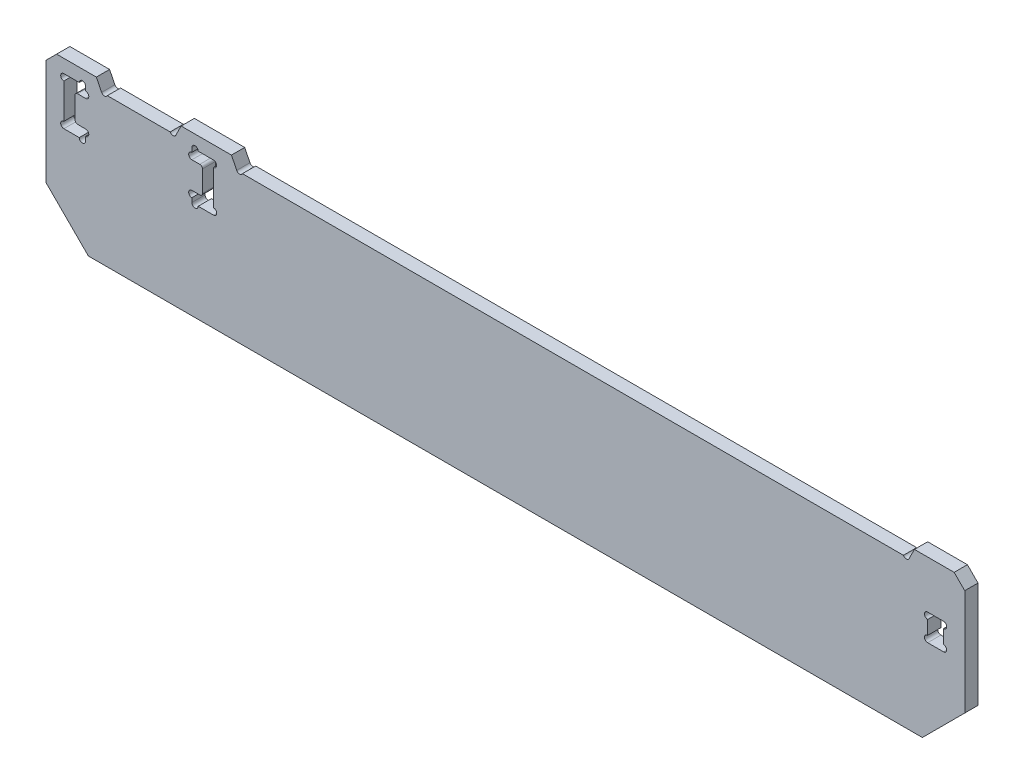
SolidWorks part; units mm, degrees
ref_plane "前视基准面" through (0, 0, 0) normal (0, 0, 1) x (1, 0, 0)
ref_plane "上视基准面" through (0, 0, 0) normal (0, 1, 0) x (1, 0, 0)
ref_plane "右视基准面" through (0, 0, 0) normal (1, 0, 0) x (0, 0, -1)
sketch "草图1" plane through (0, 0, 0) normal (0, 0, 1) x (1, 0, 0)
  line L0 (86.7, 0) -> (-86.7, 0)
  line L1 (-86.7, 0) -> (-86.7, -30)
  line L2 (-86.7, -30) -> (86.7, -30)
  line L3 (86.7, -30) -> (86.7, 0)
  point P4 (0, 0)
  dimension "D1" = 173.4
  dimension "D2" = 30
extrude "凸台-拉伸1" add sketch "草图1" along normal mid plane 2.5
chamfer "倒角1" distance 8 angle 45 2 edges at (86.7, -30, 0) (-86.7, -30, 0)
chamfer "倒角2" distance 2 angle 45 2 edges at (86.7, 0, 0) (-86.7, 0, 0)
sketch "草图2" plane through (0, 0, 1.25) normal (0, 0, 1) x (1, 0, 0)
  line L0 (-77.2, 0) -> (-76.2, -2)
  line L1 (84.7, 0) -> (-84.7, 0) construction
  line L2 (-76.2, -2) -> (-62.2, -2)
  line L3 (-62.2, -2) -> (-61.2, 0)
  line L4 (-61.2, 0) -> (-77.2, 0)
  line L6 (-86.7, -2) -> (-86.7, -22) construction
  point P8 (-69.2, 0)
  dimension "D1" = 2
  dimension "D2" = 16
  dimension "D3" = 14
  dimension "D4" = 17.5
extrude "切除-拉伸1" cut sketch "草图2" against normal through all
sketch "草图6" plane through (0, 0, 1.25) normal (0, 0, 1) x (1, 0, 0)
  line L0 (-51.7, 0) -> (-50.7, -2)
  line L1 (84.7, 0) -> (-61.2, 0) construction
  line L2 (-50.7, -2) -> (76.2, -2)
  line L3 (76.2, -2) -> (77.2, 0)
  line L4 (-51.7, 0) -> (77.2, 0)
  line L5 (-76.2, -2) -> (-62.2, -2) construction
  line L6 (-77.2, 0) -> (-76.2, -2) construction
  point P4 (0, 0)
  dimension "D1" = 7.5
  dimension "D2" = 9.5
extrude "切除-拉伸4" cut sketch "草图6" against normal through all
sketch "草图4" plane through (0, 0, 1.25) normal (0, 0, 1) x (1, 0, 0)
  line L0 (-83.325, -2.5) -> (-79.225, -2.5)
  line L1 (-79.225, -2.5) -> (-79.225, -4.5)
  line L2 (-79.225, -4.5) -> (-81.225, -4.5)
  line L3 (-81.225, -4.5) -> (-81.225, -9.5)
  line L4 (-81.225, -9.5) -> (-79.225, -9.5)
  line L5 (-79.225, -9.5) -> (-79.225, -11.5)
  line L6 (-79.225, -11.5) -> (-83.325, -11.5)
  line L7 (-83.325, -11.5) -> (-83.325, -2.5)
  line L8 (-69.2, -2.5) -> (-69.2, -11.5) construction
  line L9 (-76.2, -2) -> (-62.2, -2) construction
  line L11 (-59.175, -11.5) -> (-55.075, -11.5)
  line L12 (-59.175, -9.5) -> (-59.175, -11.5)
  line L13 (-57.175, -9.5) -> (-59.175, -9.5)
  line L14 (-57.175, -4.5) -> (-57.175, -9.5)
  line L15 (-59.175, -4.5) -> (-57.175, -4.5)
  line L16 (-59.175, -2.5) -> (-59.175, -4.5)
  line L17 (-55.075, -2.5) -> (-59.175, -2.5)
  line L18 (-55.075, -11.5) -> (-55.075, -2.5)
  line L19 (84.7, 0) -> (77.2, 0) construction
  point P10 (0, 0)
  point P13 (-69.2, -2)
  dimension "D1" = 5
  dimension "D2" = 9
  dimension "D3" = 20.05
  dimension "D4" = 2
  dimension "D5" = 2.1
  dimension "D6" = 2.5
extrude "切除-拉伸2" cut sketch "草图4" against normal through all
sketch "草图5" plane through (0, 0, 1.25) normal (0, 0, 1) x (1, 0, 0)
  line L0 (-83.325, -2.5) -> (-83.325, -11.5) construction
  line L1 (-83.325, -11.5) -> (-79.225, -11.5) construction
  line L2 (-79.225, -11.5) -> (-79.225, -9.5) construction
  line L3 (76.2, -2) -> (77.2, 0) construction
  line L4 (-79.225, -2.5) -> (-83.325, -2.5) construction
  line L5 (-55.075, -2.5) -> (-59.175, -2.5) construction
  line L6 (-59.175, -2.5) -> (-59.175, -4.5) construction
  line L7 (-59.175, -9.5) -> (-59.175, -11.5) construction
  line L8 (-59.175, -11.5) -> (-55.075, -11.5) construction
  line L9 (-55.075, -11.5) -> (-55.075, -2.5) construction
  line L10 (-79.225, -4.5) -> (-79.225, -2.5) construction
  line L11 (-51.7, 0) -> (-50.7, -2) construction
  line L12 (-77.2, 0) -> (-76.2, -2) construction
  line L13 (-62.2, -2) -> (-61.2, 0) construction
  circle A0 centre (-83.325, -3.1) radius 0.6
  circle A1 centre (-83.325, -10.9) radius 0.6
  circle A2 centre (-79.825, -11.5) radius 0.6
  circle A3 centre (-79.225, -10.1) radius 0.6
  circle A4 centre (-79.225, -3.9) radius 0.6
  circle A5 centre (-79.825, -2.5) radius 0.6
  circle A6 centre (-58.575, -2.5) radius 0.6
  circle A7 centre (-59.175, -3.9) radius 0.6
  circle A8 centre (-59.175, -10.1) radius 0.6
  circle A9 centre (-58.575, -11.5) radius 0.6
  circle A10 centre (-55.075, -10.9) radius 0.6
  circle A11 centre (-55.075, -3.1) radius 0.6
  circle A12 centre (-75.6633, -1.7317) radius 0.6
  circle A13 centre (-62.7367, -1.7317) radius 0.6
  circle A14 centre (-50.1633, -1.7317) radius 0.6
  circle A15 centre (75.6633, -1.7317) radius 0.6
  dimension "D1" = 1.2
extrude "切除-拉伸3" cut sketch "草图5" against normal through all
fillet "圆角1" radius 0.5 4 edges at (-57.175, -9.5, 0) (-57.175, -4.5, 0) (-81.225, -9.5, 0) (-81.225, -4.5, 0)
sketch "草图7" plane through (0, 0, 1.25) normal (0, 0, 1) x (1, 0, 0)
  line L0 (86.7, -22) -> (86.7, -2) construction
  line L1 (79.7, -9) -> (82.7, -9)
  line L2 (79.7, -9) -> (79.7, -14)
  line L3 (79.7, -14) -> (82.7, -14)
  line L4 (82.7, -9) -> (82.7, -14)
  line L5 (79.7, -9) -> (82.7, -14) construction
  line L6 (79.7, -14) -> (82.7, -9) construction
  line L7 (84.7, 0) -> (77.2, 0) construction
  point P0 (81.2, -11.5)
  dimension "D1" = 5.5
  dimension "D2" = 3
  dimension "D3" = 5
  dimension "D4" = 9
extrude "切除-拉伸5" cut sketch "草图7" against normal through all
sketch "草图8" plane through (0, 0, 1.25) normal (0, 0, 1) x (1, 0, 0)
  line L0 (79.7, -9) -> (79.7, -14) construction
  line L1 (82.7, -14) -> (82.7, -9) construction
  circle A0 centre (79.7, -9.6) radius 0.6
  circle A1 centre (79.7, -13.4) radius 0.6
  circle A2 centre (82.7, -13.4) radius 0.6
  circle A3 centre (82.7, -9.6) radius 0.6
  dimension "D1" = 1.2
extrude "切除-拉伸6" cut sketch "草图8" against normal through all
